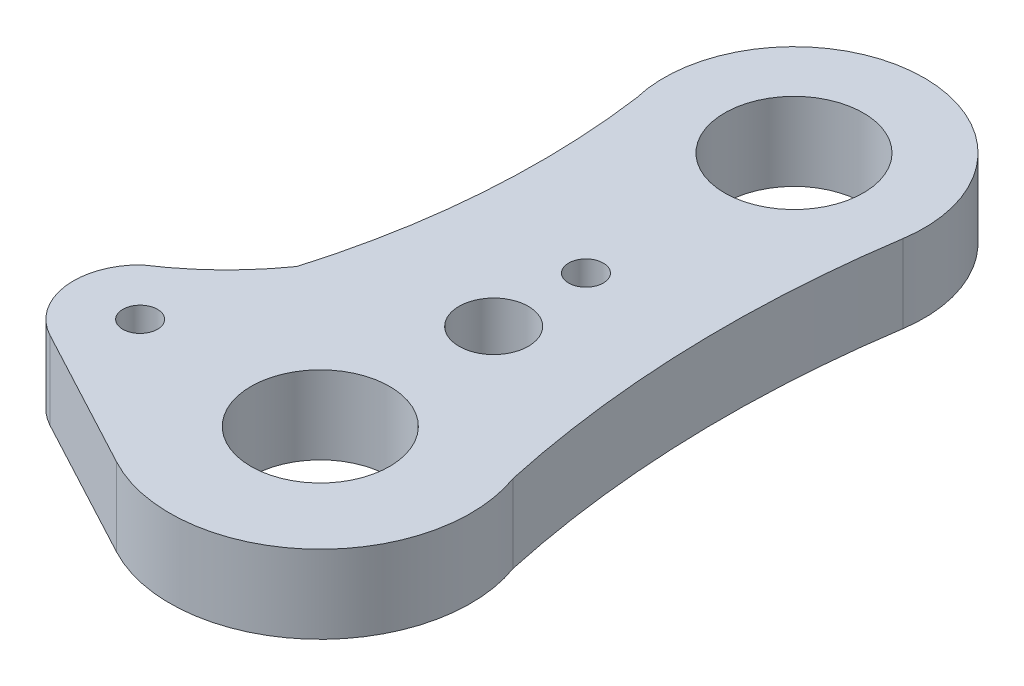
SolidWorks part; units mm, degrees
ref_plane "Front Plane" through (0, 0, 0) normal (0, 0, 1) x (1, 0, 0)
ref_plane "Top Plane" through (0, 0, 0) normal (0, 1, 0) x (1, 0, 0)
ref_plane "Right Plane" through (0, 0, 0) normal (1, 0, 0) x (0, 0, -1)
sketch "Sketch1" plane through (0, 0, 0) normal (0, 1, 0) x (1, 0, 0)
  line L0 (-23.0289, 0.5488) -> (29.7086, 0.5488) construction
  line L3 (-12.3585, -18.5583) -> (-4.0891, -22.9757)
  circle A0 centre (0, 0) radius 1
  circle A1 centre (0, 12) radius 4
  circle A2 centre (0, -5.321) radius 2
  circle A3 centre (0, -15.321) radius 4
  arc A4 (-4.0891, -22.9757) -> (8.1545, -12.3513) centre (0, -15.321) ccw
  arc A5 (7.4199, 10.8559) -> (-7.2935, 10.2202) centre (0, 12) ccw
  circle A6 centre (-10.5464, -15.166) radius 1
  arc A7 (-12.2536, -11.7197) -> (-12.3585, -18.5583) centre (-10.5464, -15.166) ccw
  arc A8 (-7.2935, 10.2202) -> (-8.6624, -8.0048) centre (-50.2167, 4.2802) cw
  arc A9 (7.4199, 10.8559) -> (8.1545, -12.3513) centre (70.6175, 1.2413) ccw
  arc A10 (-8.6624, -8.0048) -> (-13.2166, -12.398) centre (-22.4441, 1.7246) cw
  point P12 (-0.3241, 19.5006)
  point P15 (0, -23.9994)
  dimension "D1" = 43.5
  dimension "D2" = 8
  dimension "D3" = 4
  dimension "D4" = 8
  dimension "D5" = 2
  dimension "D6" = 2
  dimension "D7" = 10
  dimension "D8" = 12
extrude "Boss-Extrude1" add sketch "Sketch1" along normal blind 4.5 contours L0 A8 A10 A7 L3 A4 A9 A0 A2 A3 A6 | A8 L0 A0 A9 A5 A1
